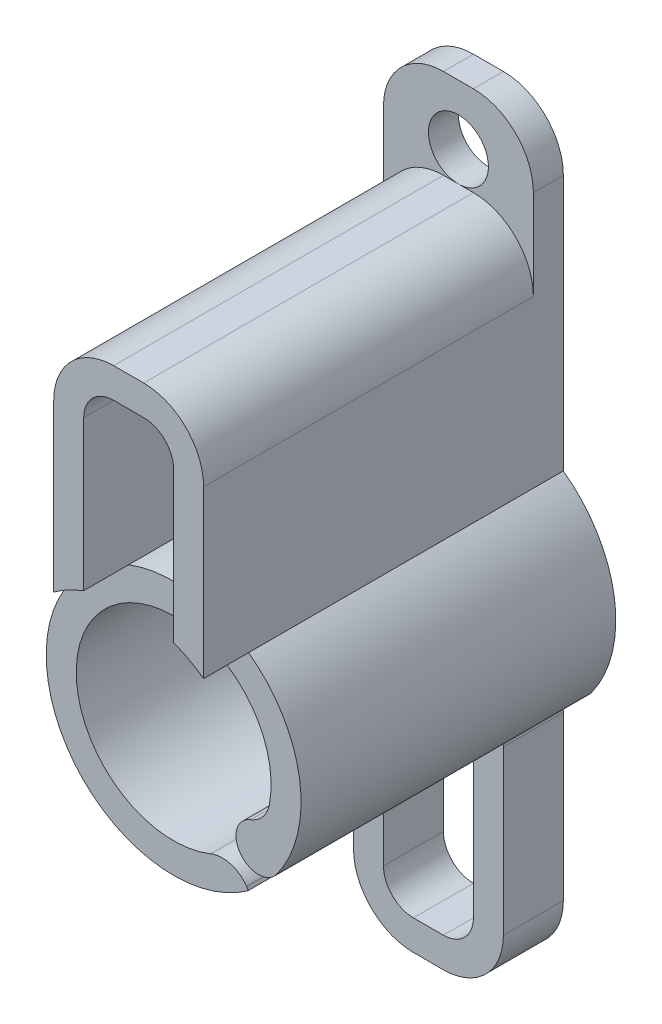
SolidWorks part; units mm, degrees
ref_plane "Ön Düzlem" through (0, 0, 0) normal (0, 0, 1) x (1, 0, 0)
ref_plane "Üst Düzlem" through (0, 0, 0) normal (0, 1, 0) x (1, 0, 0)
ref_plane "Sağ Düzlem" through (0, 0, 0) normal (1, 0, 0) x (0, 0, -1)
sketch "Çizim1" plane through (0, 0, 0) normal (0, 0, 1) x (1, 0, 0)
  line L0 (0, 0) -> (0, -25.8421) construction
  line L1 (0, 0) -> (27.9398, 0) construction
  line L2 (-2.5, 3.4369) -> (-2.5, 8.9765)
  line L3 (-0.5, 10.9765) -> (0.5, 10.9765)
  line L4 (2.5, 3.4369) -> (2.5, 8.9765)
  line L5 (-1.5, 3.9765) -> (-1.5, 8.9765)
  line L6 (-0.5, 9.9765) -> (0.5, 9.9765)
  line L7 (1.5, 3.9765) -> (1.5, 8.9765)
  line L8 (2.4426, -3.358) -> (2.4298, -3.3404)
  line L9 (1.5, -3.9765) -> (1.5, -8.9765)
  line L10 (-0.5, -9.9765) -> (0.5, -9.9765)
  line L11 (-1.5, -3.9765) -> (-1.5, -8.9765)
  line L12 (2.5, -3.5345) -> (2.5, -8.9765)
  line L13 (-0.5, -10.9765) -> (0.5, -10.9765)
  line L14 (-2.5, -3.4369) -> (-2.5, -8.9765)
  arc A0 (3.1923, -0.6098) -> (1.2397, -3.0043) centre (0, 0) ccw
  arc A1 (-2.5, 3.4369) -> (-2.5, -3.4369) centre (0, 0) ccw
  arc A2 (-2.5, 8.9765) -> (-0.5, 10.9765) centre (-0.5, 8.9765) cw
  arc A3 (0.5, 10.9765) -> (2.5, 8.9765) centre (0.5, 8.9765) cw
  arc A4 (0.5, 9.9765) -> (1.5, 8.9765) centre (0.5, 8.9765) cw
  arc A5 (-1.5, 8.9765) -> (-0.5, 9.9765) centre (-0.5, 8.9765) cw
  arc A6 (1.5, 3.9765) -> (-1.5, 3.9765) centre (0, 0) ccw
  arc A7 (1.5, -3.9765) -> (-1.5, -3.9765) centre (0, 0) cw
  arc A8 (-1.5, -8.9765) -> (-0.5, -9.9765) centre (-0.5, -8.9765) ccw
  arc A9 (0.5, -9.9765) -> (1.5, -8.9765) centre (0.5, -8.9765) ccw
  arc A10 (0.5, -10.9765) -> (2.5, -8.9765) centre (0.5, -8.9765) ccw
  arc A11 (-2.5, -8.9765) -> (-0.5, -10.9765) centre (-0.5, -8.9765) ccw
  arc A12 (-1.5, -3.9765) -> (1.5, -3.9765) centre (0, 0) ccw
  arc A13 (3.4373, -2.4995) -> (2.5, 3.4369) centre (0, 0) ccw
  arc A14 (2.4298, -3.3404) -> (1.2397, -3.0043) centre (1.6211, -3.9287) ccw
  arc A15 (3.1923, -0.6098) -> (2.5647, -1.3571) centre (2.21, -0.4222) cw
  arc A16 (2.5, -3.5345) -> (2.4426, -3.358) centre (2.2, -3.5345) ccw
  arc A17 (2.5647, -1.3571) -> (3.4373, -2.4995) centre (2.8307, -2.0584) ccw
  point P38 (1.5, -9.9765)
  dimension "D1" = 1
  dimension "D2" = 1
  dimension "D3" = 1.5
  dimension "D4" = 1
  dimension "D5" = 0.3
extrude "Yükseklik-Ekstrüzyon1" add sketch "Çizim1" along normal blind 12 contours A15 A17 A13 L4 A3 L3 A2 L2 A1 L14 A11 L13 A10 L12 A16 L8 A14 A0 L7 A6 L5 A5 L6 A4 A9 L10 A8 L11 A7 L9
sketch "Çizim2" plane through (0, 0, 12) normal (0, 0, 1) x (1, 0, 0)
  line L0 (2.5, -3.5345) -> (2.5, -8.9765) construction
  line L2 (-2.5, -3.4369) -> (-2.5, -10.9765)
  line L3 (-2.5, -10.9765) -> (2.5, -10.9765)
  line L4 (2.5, -3.4369) -> (2.5, -10.9765)
  line L5 (-0.5, -10.9765) -> (0.5, -10.9765) construction
  arc A0 (-2.5, -3.4369) -> (2.5, -3.4369) centre (0, 0) ccw
extrude "Kes-Ekstrüzyon1" cut sketch "Çizim2" against normal blind 10
sketch "Çizim3" plane through (0, 0, 0) normal (0, 0, -1) x (-1, 0, 0)
  line L0 (2.5, 3.4369) -> (2.5, 8.9765) construction
  line L1 (-2.5, 8.9765) -> (-1.5, 8.9765)
  line L2 (-2.5, 8.9765) -> (-2.5, 11.9765)
  line L3 (-0.5, 13.9765) -> (0.5, 13.9765)
  line L4 (2.5, 8.9765) -> (2.5, 11.9765)
  line L8 (-0.5, 9.9765) -> (0.5, 9.9765)
  line L9 (1.5, 8.9765) -> (2.5, 8.9765)
  arc A0 (0.5, 13.9765) -> (2.5, 11.9765) centre (0.5, 11.9765) cw
  arc A1 (-2.5, 11.9765) -> (-0.5, 13.9765) centre (-0.5, 11.9765) cw
  arc A2 (-0.5, 9.9765) -> (-1.5, 8.9765) centre (-0.5, 8.9765) ccw
  arc A3 (0.5, 9.9765) -> (1.5, 8.9765) centre (0.5, 8.9765) cw
  arc A4 (-0.5, 9.9765) -> (-1.5, 8.9765) centre (-0.5, 8.9765) ccw construction
  point P9 (2.5, 13.9765)
  arc M25 (2.5, 8.9765) -> (0.5, 10.9765) centre (0.5, 8.9765) ccw
  line M26 (0.5, 10.9765) -> (-0.5, 10.9765)
  arc M27 (-0.5, 10.9765) -> (-2.5, 8.9765) centre (-0.5, 8.9765) ccw
  dimension "D2" = 2
  dimension "D1" = 5
extrude "Yükseklik-Ekstrüzyon7" add sketch "Çizim3" against normal blind 1 contours A1 L2 L4 A0 L3 M27 M26 M25
sketch "Çizim4" plane through (0, 0, 0) normal (0, 0, -1) x (-1, 0, 0)
  line L0 (0, 8.9444) -> (0, 11.4032) construction
  line L1 (0, 11.9765) -> (3.7301, 11.9765) construction
  circle A0 centre (0, 11.9765) radius 1
  dimension "D1" = 2
extrude "Kes-Ekstrüzyon2" cut sketch "Çizim4" against normal blind 11
ref_plane "Düzlem1" through (0, 0, 12) normal (0, 0, 1) x (1, 0, 0)
sketch "Çizim6" plane through (0, 0, 12) normal (0, 0, 1) x (1, 0, 0)
  line L0 (0, 0) -> (0, -8.1578) construction
  line L1 (0, 0) -> (12.6028, 0) construction
  circle A0 centre (0, 0) radius 4.25
extrude "Kes-Ekstrüzyon3" cut sketch "Çizim6" against normal blind 1.5
